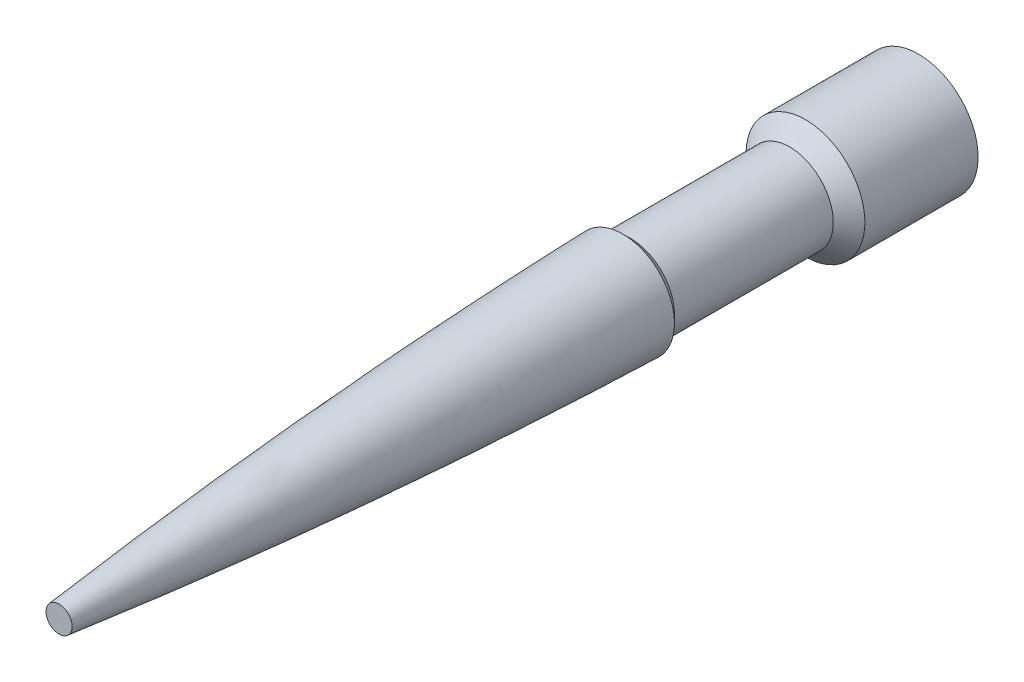
SolidWorks part; units mm, degrees
ref_plane "Front Plane" through (0, 0, 0) normal (0, 0, 1) x (1, 0, 0)
ref_plane "Top Plane" through (0, 0, 0) normal (0, 1, 0) x (1, 0, 0)
ref_plane "Right Plane" through (0, 0, 0) normal (1, 0, 0) x (0, 0, -1)
sketch "Sketch1" plane through (0, 0, 0) normal (0, 1, 0) x (1, 0, 0)
  line L0 (-1316.6724, 416.1597) -> (48.661, 416.1597) construction
  line L1 (0, 0) -> (0, -108.4931)
  line L2 (0, 0) -> (7.5, 0)
  line L3 (7.5, 0) -> (7.5, -14.293)
  line L4 (7.5, -14.293) -> (5.5082, -16.2847)
  line L5 (5.5082, -16.2847) -> (5.5082, -36.3347)
  line L6 (5.5082, -36.3347) -> (6.5041, -37.3306)
  line L7 (0, -108.4931) -> (1.648, -108.4931)
  spline S0 degree 2 poles (6.5041, -37.3306) (5.5452, -73.0165) (1.648, -108.4931) knots 0 0 0 1 1 1
revolve "Revolve1" add sketch "Sketch1" angle 360 about L1
